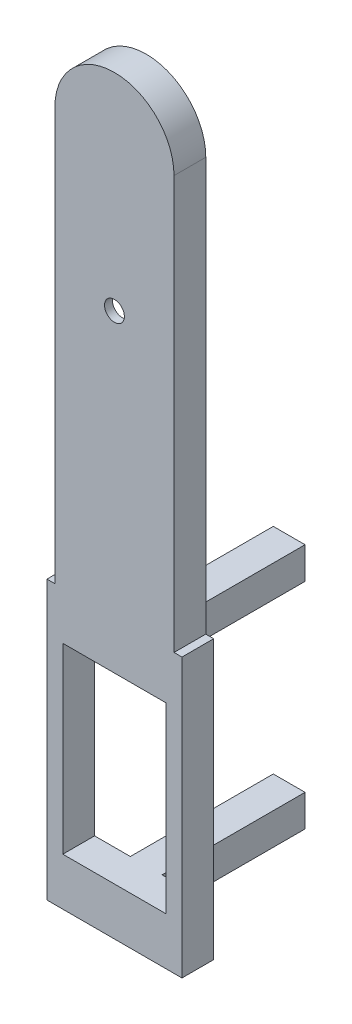
SolidWorks part; units mm, degrees
ref_plane "前基準面" through (0, 0, 0) normal (0, 0, 1) x (1, 0, 0)
ref_plane "上基準面" through (0, 0, 0) normal (0, 1, 0) x (1, 0, 0)
ref_plane "右基準面" through (0, 0, 0) normal (1, 0, 0) x (0, 0, -1)
sketch "草圖1" plane through (0, 0, 0) normal (0, 0, 1) x (1, 0, 0)
  line L0 (0, 0) -> (0, 4.6483) construction
  line L1 (7.5, 0) -> (7.5, 52)
  line L2 (7.5, 0) -> (-7.5, 0)
  line L3 (-7.5, 0) -> (-7.5, 52)
  arc A0 (7.5, 52) -> (-7.5, 52) centre (0, 52) ccw
  dimension "D1" = 7.5
  dimension "D2" = 52
extrude "填料-伸長1" add sketch "草圖1" along normal blind 4
sketch "草圖3" plane through (0, 0, 0) normal (0, 0, 1) x (1, 0, 0)
  line L0 (0, 0) -> (0, 15.7412) construction
  line L1 (7.5, 52) -> (-7.5, 52) construction
  line L2 (7.5, 15) -> (-7.5, 15) construction
  line L3 (7.5, 0) -> (7.5, 52) construction
  line L4 (-7.5, 52) -> (-7.5, 0) construction
  line L5 (-7.5, 0) -> (7.5, 0) construction
  line L6 (7.5, 33.5) -> (5, 33.5) construction
  line L7 (5, 33.5) -> (2.4679, 17.8421)
  line L8 (5, 33.5) -> (2.5, 48.7588)
  line L9 (-2.5, 48.7588) -> (-5, 33.5)
  line L10 (-5, 33.5) -> (-2.5, 18.2412)
  line L11 (0, 51.2588) -> (0, 59.5) construction
  line L12 (-5, 33.5) -> (-7.5, 33.5) construction
  arc A0 (7.5, 52) -> (-7.5, 52) centre (0, 52) ccw construction
  arc A1 (-4.7386, 35.0956) -> (-4.7386, 31.9044) centre (0, 33.5) ccw
  arc A2 (-2.5, 18.2412) -> (2.4679, 17.8421) centre (0, 18.2412) ccw
  arc A3 (-2.5, 48.7588) -> (2.5, 48.7588) centre (0, 48.7588) cw
  arc A4 (4.7452, 31.9241) -> (4.7386, 35.0956) centre (0, 33.5) ccw
  dimension "D4" = 10
  dimension "D1" = 15
  dimension "D2" = 37
  dimension "D3" = 18.5
extrude "除料-伸長1" cut sketch "草圖3" along normal blind 3 contours A3 L9 L10 A2 L7 L8
sketch "草圖5" plane through (0, 0, 0) normal (0, 0, 1) x (1, 0, 0)
  line L0 (5, 33.5) -> (-5, 33.5) construction
  circle A0 centre (0, 33.5) radius 1.25
  dimension "D1" = 2.5
extrude "除料-伸長2" cut sketch "草圖5" along normal blind 12.4
sketch "草圖6" plane through (0, 0, 0) normal (0, 0, 1) x (1, 0, 0)
  line L0 (0, 62.3953) -> (0, -4.428) construction
  line L1 (0, -2.2) -> (0, 2.2) construction
  line L3 (8.5, 0) -> (-8.5, 0)
  line L4 (8.5, 0) -> (8.5, -35)
  line L5 (8.5, -35) -> (-8.5, -35)
  line L6 (-8.5, 0) -> (-8.5, -35)
  dimension "D1" = 17
  dimension "D2" = 8.5
  dimension "D3" = 35
extrude "填料-伸長2" add sketch "草圖6" along normal blind 4
sketch "草圖7" plane through (0, 0, 0) normal (0, 0, 1) x (1, 0, 0)
  line L0 (0, 64.1958) -> (0, -38.5274) construction
  line L1 (0, -2.2) -> (0, 2.2) construction
  line L3 (-6.5, -6) -> (6.5, -6)
  line L4 (-6.5, -6) -> (-6.5, -29)
  line L5 (-6.5, -29) -> (6.5, -29)
  line L6 (6.5, -6) -> (6.5, -29)
  line L7 (-8.5, -35) -> (8.5, -35) construction
  dimension "D1" = 6.5
  dimension "D2" = 13
  dimension "D3" = 23
  dimension "D4" = 6
extrude "除料-伸長3" cut sketch "草圖7" along normal blind 12.1
sketch "草圖8" plane through (0, 0, 0) normal (0, 0, 1) x (1, 0, 0)
  line L0 (0, 64.1958) -> (0, -34.8274) construction
  line L1 (0, -2.2) -> (0, 2.2) construction
  line L2 (0, 64.1958) -> (0, -39.0142) construction
  line L3 (6.5, -17.5) -> (-6.5, -17.5) construction
  line L4 (6.5, -29) -> (6.5, -6) construction
  line L5 (-6.5, -6) -> (-6.5, -29) construction
  line L6 (6.5, -6) -> (-6.5, -6) construction
  line L7 (2, -2) -> (-2, -2)
  line L8 (2, -2) -> (2, -6)
  line L9 (2, -6) -> (-2, -6)
  line L10 (-2, -2) -> (-2, -6)
  line L11 (2, -29) -> (-2, -29)
  line L12 (-2, -33) -> (-2, -29)
  line L13 (2, -33) -> (-2, -33)
  line L14 (2, -33) -> (2, -29)
  circle A0 centre (0, -4) radius 1.25
  circle A1 centre (0, -31) radius 1.25
  dimension "D5" = 2.5
  dimension "D1" = 4
  dimension "D2" = 4
  dimension "D3" = 2
  dimension "D4" = 2
extrude "填料-伸長3" add sketch "草圖8" against normal blind 18
